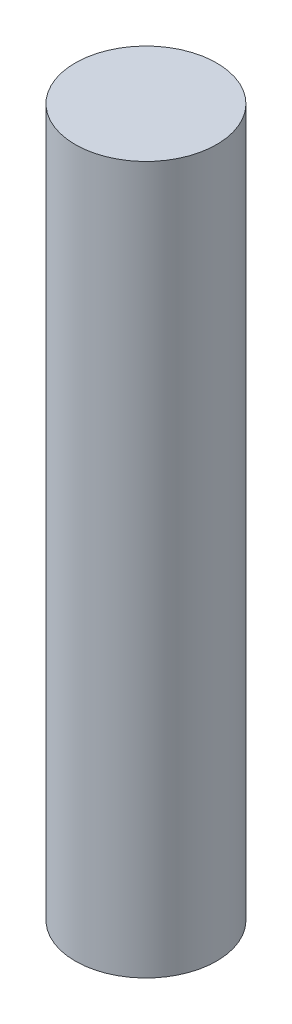
SolidWorks part; units mm, degrees
ref_plane "Front Plane" through (0, 0, 0) normal (0, 0, 1) x (1, 0, 0)
ref_plane "Top Plane" through (0, 0, 0) normal (0, 1, 0) x (1, 0, 0)
ref_plane "Right Plane" through (0, 0, 0) normal (1, 0, 0) x (0, 0, -1)
sketch "Sketch1" plane through (0, 0, 0) normal (0, 1, 0) x (1, 0, 0)
  circle A0 centre (0, 0) radius 3
  dimension "D1" = 6
extrude "Boss-Extrude1" add sketch "Sketch1" along normal blind 30
